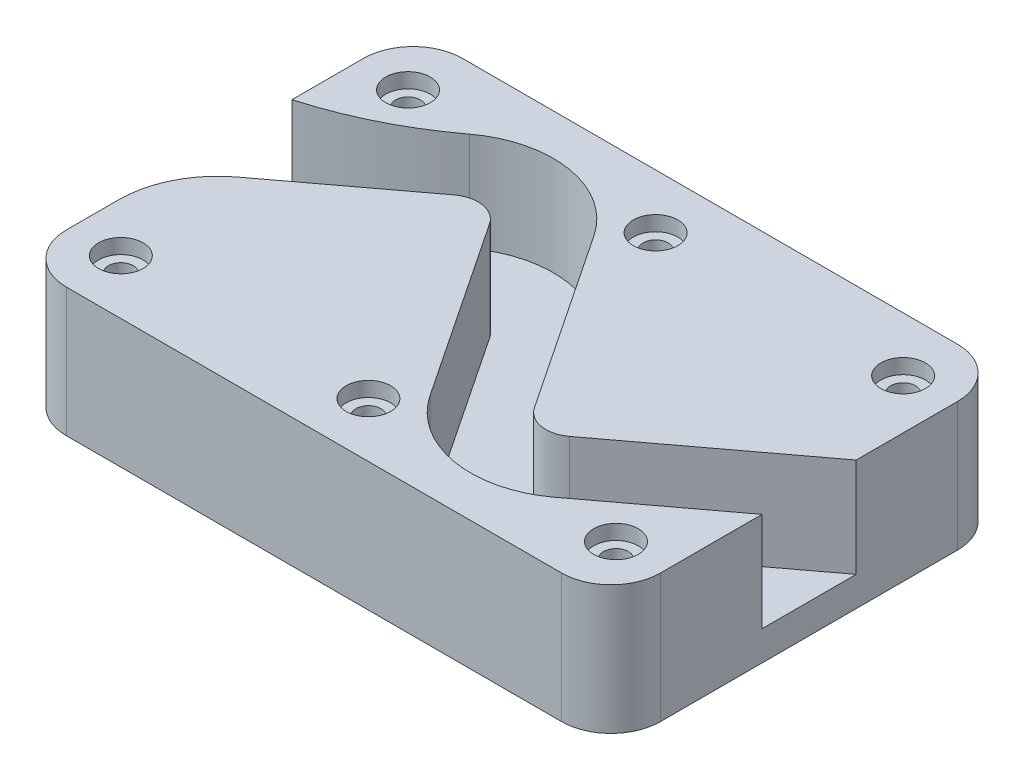
SolidWorks part; units mm, degrees
ref_plane "Front Plane" through (0, 0, 0) normal (0, 0, 1) x (1, 0, 0)
ref_plane "Top Plane" through (0, 0, 0) normal (0, 1, 0) x (1, 0, 0)
ref_plane "Right Plane" through (0, 0, 0) normal (1, 0, 0) x (0, 0, -1)
sketch "Sketch1" plane through (0, 0, 0) normal (0, 1, 0) x (1, 0, 0)
  line L1 (-63.5, -50.8) -> (63.5, -50.8)
  line L2 (-76.2, -38.1) -> (-76.2, 38.1)
  line L3 (-63.5, 50.8) -> (63.5, 50.8)
  line L4 (76.2, -38.1) -> (76.2, 38.1)
  line L5 (-76.2, -50.8) -> (76.2, 50.8) construction
  line L6 (-76.2, 50.8) -> (76.2, -50.8) construction
  arc A0 (-63.5, 50.8) -> (-76.2, 38.1) centre (-63.5, 38.1) ccw
  arc A1 (-63.5, -50.8) -> (-76.2, -38.1) centre (-63.5, -38.1) cw
  arc A2 (76.2, -38.1) -> (63.5, -50.8) centre (63.5, -38.1) cw
  arc A3 (76.2, 38.1) -> (63.5, 50.8) centre (63.5, 38.1) ccw
  point P0 (0, 0)
  dimension "D3" = 12.7
  dimension "D4" = 12.7
  dimension "D5" = 12.7
  dimension "D6" = 12.7
  dimension "D1" = 101.6
  dimension "D2" = 152.4
extrude "Boss-Extrude1" add sketch "Sketch1" along normal blind 33.02
sketch "Sketch2" plane through (0, 33.02, 0) normal (0, 1, 0) x (1, 0, 0)
  line L0 (-87.0738, 0) -> (92.4146, 0) construction
  line L1 (0, 60.8556) -> (0, -58.483) construction
  line L2 (-25.4, 60.8556) -> (-25.4, -58.483) construction
  line L3 (25.4, 60.8556) -> (25.4, -58.483) construction
  line L4 (63.5, 50.8) -> (-63.5, 50.8) construction
  line L5 (63.5, 50.8) -> (-63.5, 50.8) construction
  line L6 (-76.2, 0) -> (-25.4, 38.1) construction
  line L8 (63.5, 38.1) -> (-63.5, 38.1) construction
  line L10 (-63.5, -50.8) -> (63.5, -50.8) construction
  line L11 (-63.5, -50.8) -> (63.5, -50.8) construction
  line L12 (-63.5, -38.1) -> (63.5, -38.1) construction
  line L13 (-25.4, 38.1) -> (25.4, -38.1) construction
  line L14 (-76.2, 19.7593) -> (-76.2, -24.765)
  line L15 (76.2, -38.1) -> (76.2, 38.1) construction
  line L16 (76.2, -38.1) -> (76.2, 38.1) construction
  line L17 (25.4, -38.1) -> (76.2, 0) construction
  line L18 (-66.04, -4.445) -> (-34.2154, 19.4235)
  line L20 (-7.2412, 28.2622) -> (23.3031, -17.5543)
  line L21 (-23.3031, 17.5543) -> (7.2412, -28.2622)
  line L22 (45.7978, -34.8667) -> (76.2, -12.065)
  line L23 (34.2154, -19.4235) -> (76.2, 12.065)
  line L26 (-76.2, -24.765) -> (-76.2, -38.1) construction
  line L27 (-101.9688, 109.7614) -> (-45.7978, 34.8667) construction
  line L31 (76.2, 12.065) -> (76.2, -12.065)
  arc A0 (-45.7978, 34.8667) -> (-76.2, 19.7593) centre (-101.9688, 109.7614) cw
  arc A1 (-76.2, -24.765) -> (-66.04, -4.445) centre (-50.8, -24.765) cw
  arc A2 (-34.2154, 19.4235) -> (-23.3031, 17.5543) centre (-29.6434, 13.3275) cw
  arc A3 (-45.7978, 34.8667) -> (-7.2412, 28.2622) centre (-29.6434, 13.3275) cw
  arc A4 (34.2154, -19.4235) -> (23.3031, -17.5543) centre (29.6434, -13.3275) cw
  arc A5 (45.7978, -34.8667) -> (7.2412, -28.2622) centre (29.6434, -13.3275) cw
  dimension "D6" = 26.924
  dimension "D5" = 7.62
  dimension "D9" = 26.924
  dimension "D10" = 19.304
  dimension "D8" = 7.62
  dimension "D4" = 12.7
  dimension "D7" = 19.304
  dimension "D1" = 12.7
  dimension "D2" = 25.4
  dimension "D3" = 25.4
extrude "Cut-Extrude1" cut sketch "Sketch2" against normal blind 25.4
sketch "Sketch3" plane through (0, 33.02, 0) normal (0, 1, 0) x (1, 0, 0)
  line L0 (0, 57.0847) -> (0, -58.0401) construction
  line L1 (-94.2118, 0) -> (89.4462, 0) construction
  circle A0 centre (63.5, 36.83) radius 3.175
  circle A1 centre (0, 36.83) radius 3.175
  circle A2 centre (-63.5, 36.83) radius 3.175
  circle A3 centre (63.5, -36.83) radius 3.175
  circle A12 centre (0, -36.83) radius 3.175
  circle A13 centre (-63.5, -36.83) radius 3.175
  dimension "D2" = 6.35
extrude "Cut-Extrude2" cut sketch "Sketch3" against normal through all
sketch "Sketch4" plane through (0, 33.02, 0) normal (0, 1, 0) x (1, 0, 0)
  circle A0 centre (-63.5, 36.83) radius 3.175 construction
  circle A1 centre (0, 36.83) radius 3.175 construction
  circle A2 centre (63.5, 36.83) radius 3.175 construction
  circle A3 centre (63.5, -36.83) radius 3.175 construction
  circle A4 centre (0, -36.83) radius 3.175 construction
  circle A5 centre (-63.5, -36.83) radius 3.175 construction
  circle A6 centre (-63.5, 36.83) radius 3.175 construction
  circle A7 centre (0, 36.83) radius 3.175 construction
  circle A8 centre (63.5, 36.83) radius 3.175 construction
  circle A9 centre (63.5, -36.83) radius 3.175 construction
  circle A10 centre (0, -36.83) radius 3.175 construction
  circle A11 centre (-63.5, -36.83) radius 3.175 construction
  circle A12 centre (-63.5, 36.83) radius 5.715
  circle A13 centre (0, 36.83) radius 5.715
  circle A14 centre (63.5, 36.83) radius 5.715
  circle A15 centre (63.5, -36.83) radius 5.715
  circle A16 centre (0, -36.83) radius 5.715
  circle A17 centre (-63.5, -36.83) radius 5.715
  dimension "D1" = 2.54
extrude "Cut-Extrude3" cut sketch "Sketch4" against normal blind 3.81
